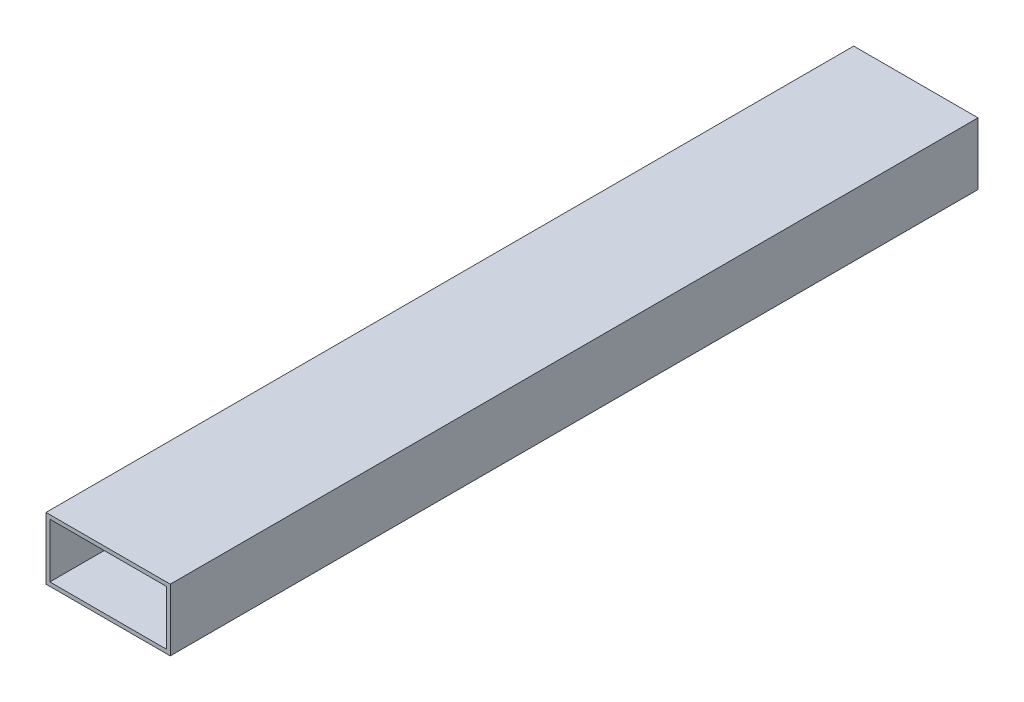
SolidWorks part; units mm, degrees
ref_plane "Front Plane" through (0, 0, 0) normal (0, 0, 1) x (1, 0, 0)
ref_plane "Top Plane" through (0, 0, 0) normal (0, 1, 0) x (1, 0, 0)
ref_plane "Right Plane" through (0, 0, 0) normal (1, 0, 0) x (0, 0, -1)
sketch "Sketch1" plane through (0, 0, 0) normal (0, 0, 1) x (1, 0, 0)
  line L0 (1.5875, 1.5875) -> (49.2125, 1.5875)
  line L1 (0, 0) -> (50.8, 0)
  line L2 (0, 0) -> (0, 25.4)
  line L3 (0, 25.4) -> (50.8, 25.4)
  line L4 (50.8, 0) -> (50.8, 25.4)
  line L5 (49.2125, 1.5875) -> (49.2125, 23.8125)
  line L6 (1.5875, 23.8125) -> (49.2125, 23.8125)
  line L7 (1.5875, 1.5875) -> (1.5875, 23.8125)
  dimension "D1" = 50.8
  dimension "D2" = 25.4
  dimension "D3" = 1.5875
extrude "Boss-Extrude1" add sketch "Sketch1" along normal blind 330.2
